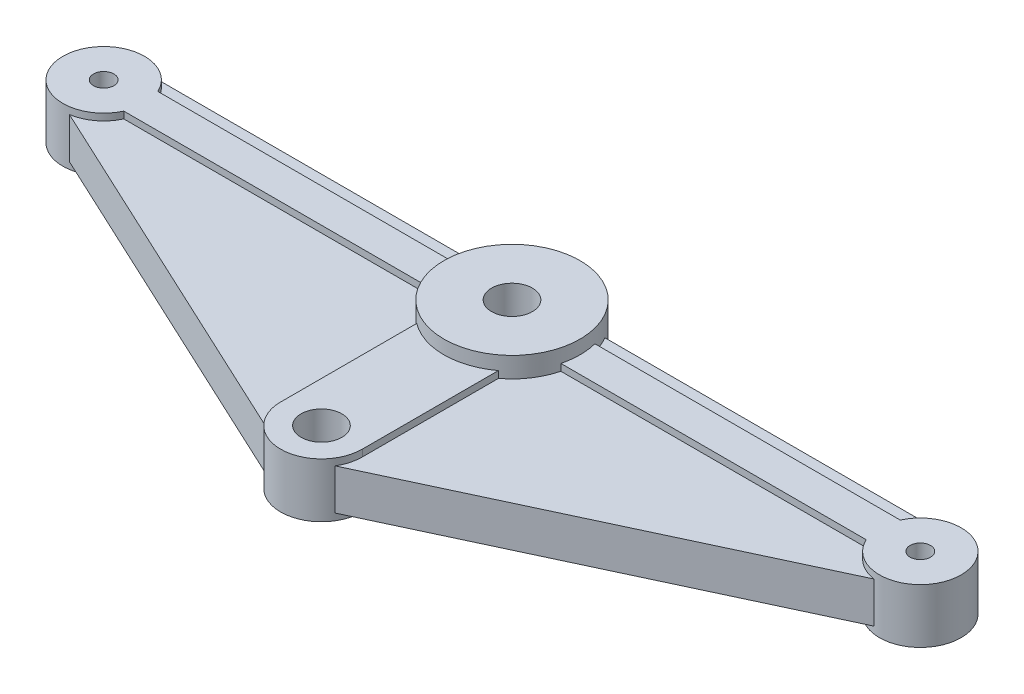
SolidWorks part; units mm, degrees
ref_plane "Front Plane" through (0, 0, 0) normal (0, 0, 1) x (1, 0, 0)
ref_plane "Top Plane" through (0, 0, 0) normal (0, 1, 0) x (1, 0, 0)
ref_plane "Right Plane" through (0, 0, 0) normal (1, 0, 0) x (0, 0, -1)
sketch "Sketch1" plane through (0, 0, 0) normal (0, 1, 0) x (1, 0, 0)
  line L0 (-30, 0) -> (30, 0) construction
  line L1 (0, 0) -> (0, -14) construction
  line L2 (-30, 2.5) -> (30, 2.5)
  line L3 (31.0572, -2.2655) -> (1.0572, -16.2655)
  line L4 (-31.0572, -2.2655) -> (-1.0572, -16.2655)
  circle A0 centre (30, 0) radius 0.75
  circle A1 centre (-30, 0) radius 0.75
  circle A2 centre (0, -14) radius 1.5
  circle A3 centre (0, 0) radius 1.5
  arc A4 (30, 2.5) -> (31.0572, -2.2655) centre (30, 0) cw
  arc A5 (-30, 2.5) -> (-31.0572, -2.2655) centre (-30, 0) ccw
  arc A6 (1.0572, -16.2655) -> (-1.0572, -16.2655) centre (0, -14) cw
  dimension "D2" = 1.5
  dimension "D3" = 3
  dimension "D4" = 3
  dimension "D6" = 2.5
  dimension "D1" = 60
  dimension "D5" = 14
extrude "Extrude1" add sketch "Sketch1" along normal mid plane 3
sketch "Sketch2" plane through (0, 0, 0) normal (0, 1, 0) x (1, 0, 0)
  line L0 (-27.2728, 1.25) -> (-0.8292, 1.25)
  line L1 (-27.2728, -1.25) -> (-3, -1.25)
  line L2 (-3, -1.25) -> (-3, -14)
  line L3 (3, -1.25) -> (3, -14)
  line L4 (3, -1.25) -> (27.2728, -1.25)
  line L5 (0.8292, 1.25) -> (27.2728, 1.25)
  arc A0 (27.2728, -1.25) -> (27.2728, 1.25) centre (30, 0) ccw
  arc A1 (-27.2728, 1.25) -> (-27.2728, -1.25) centre (-30, 0) ccw
  arc A2 (-3, -14) -> (3, -14) centre (0, -14) ccw
  arc A3 (-0.8292, 1.25) -> (0.8292, 1.25) centre (0, 0) ccw
  circle A4 centre (0, 0) radius 1.5 construction
  circle A5 centre (30, 0) radius 0.75
  circle A6 centre (0, -14) radius 1.5
  circle A7 centre (-30, 0) radius 0.75
  circle A8 centre (30, 0) radius 0.75 construction
  circle A9 centre (0, -14) radius 1.5 construction
  circle A10 centre (-30, 0) radius 0.75 construction
  dimension "D1" = 3
  dimension "D2" = 2.5
extrude "Extrude2" add sketch "Sketch2" along normal mid plane 4
sketch "Sketch3" plane through (0, 0, 0) normal (0, 1, 0) x (1, 0, 0)
  circle A0 centre (0, 0) radius 5
  circle A1 centre (0, 0) radius 1.5
  circle A2 centre (0, 0) radius 1.5 construction
  dimension "D1" = 10
extrude "Extrude3" add sketch "Sketch3" along normal mid plane 6
